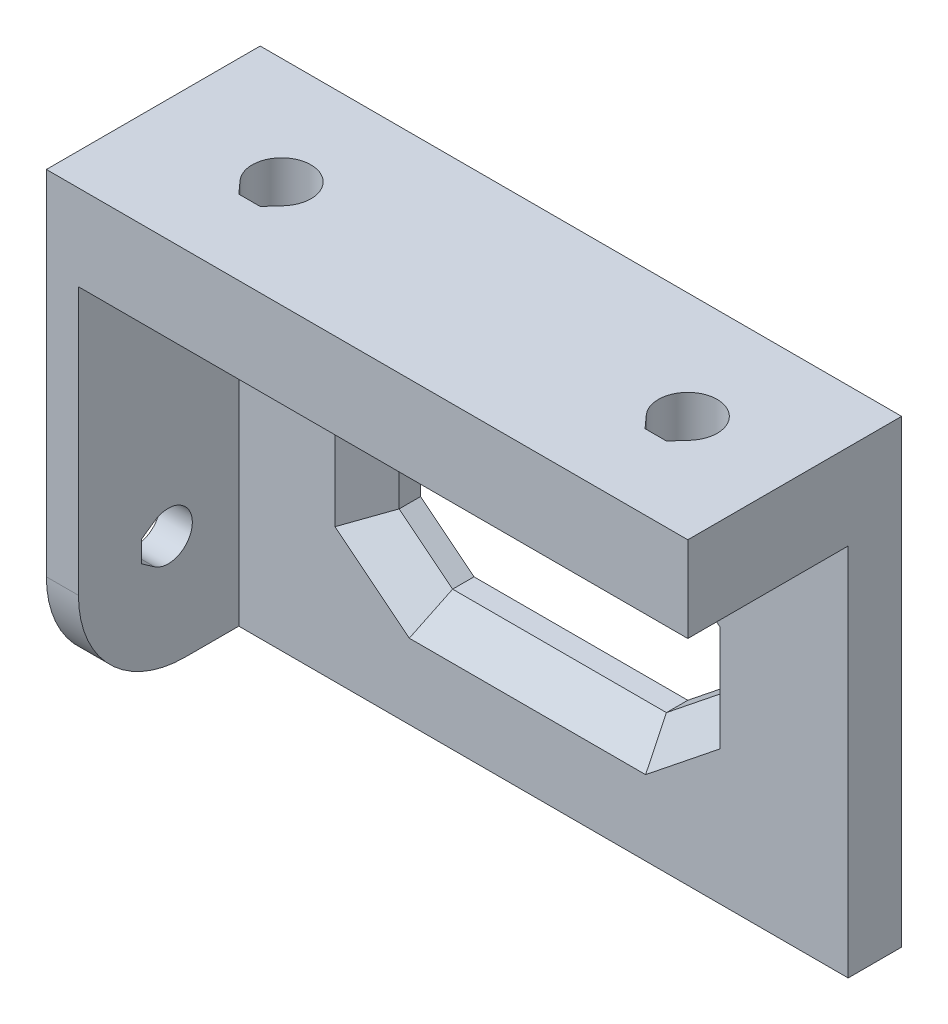
SolidWorks part; units mm, degrees
ref_plane "Alzado" through (0, 0, 0) normal (0, 0, 1) x (1, 0, 0)
ref_plane "Planta" through (0, 0, 0) normal (0, 1, 0) x (1, 0, 0)
ref_plane "Vista lateral" through (0, 0, 0) normal (1, 0, 0) x (0, 0, -1)
sketch "Croquis1" plane through (0, 0, 0) normal (0, 0, 1) x (1, 0, 0)
  line L1 (0, 0) -> (60, 0)
  line L2 (0, 0) -> (0, 35)
  line L3 (0, 35) -> (60, 35)
  line L4 (60, 0) -> (60, 35)
  line L5 (15, 25) -> (45, 25)
  line L6 (15, 25) -> (15, 10)
  line L7 (15, 10) -> (45, 10)
  line L8 (45, 25) -> (45, 10)
  dimension "D1" = 60
  dimension "D2" = 30
  dimension "D3" = 15
  dimension "D4" = 15
  dimension "D5" = 10
  dimension "D6" = 35
extrude "Saliente-Extruir1" add sketch "Croquis1" along normal blind 5
chamfer "Chaflán2" distance 4 distance2 5 2 edges at (45, 10, 2.5) (15, 25, 2.5)
chamfer "Chaflán3" distance 5 distance2 4 2 edges at (45, 25, 2.5) (15, 10, 2.5)
chamfer "Chaflán1" distance 3 angle 45 8 edges at (30, 10, 5) (45, 17.5, 5) (30, 25, 5) (15, 17.5, 5) (17.5, 12, 5) (42.5, 12, 5) (42.5, 23, 5) (17.5, 23, 5)
sketch "Croquis2" plane through (0, 0, 0) normal (0, 0, -1) x (-1, 0, 0)
  line L0 (0, 35) -> (0, 0) construction
  line L1 (-60, 35) -> (0, 35)
  line L2 (-60, 35) -> (-60, 43)
  line L3 (-60, 43) -> (0, 43)
  line L4 (0, 35) -> (0, 43)
  dimension "D1" = 8
extrude "Saliente-Extruir2" add sketch "Croquis2" against normal blind 20
sketch "Croquis3" plane through (0, 35, 0) normal (0, -1, 0) x (1, 0, 0)
  line L0 (60, 20) -> (0, 20) construction
  line L1 (9.9557, 11.8394) -> (11, 13)
  line L2 (11, 13) -> (13, 13)
  line L3 (13, 13) -> (14.0443, 11.8394)
  line L4 (12, 10) -> (12, 16.6449) construction
  line L5 (0, 20) -> (0, 5) construction
  line L6 (60, 20) -> (60, 5) construction
  line L7 (47.9557, 11.8394) -> (49, 13)
  line L8 (49, 13) -> (51, 13)
  line L9 (51, 13) -> (52.0443, 11.8394)
  line L10 (50, 10) -> (50, 14.7986) construction
  arc A0 (9.9557, 11.8394) -> (14.0443, 11.8394) centre (12, 10) ccw
  arc A1 (47.9557, 11.8394) -> (52.0443, 11.8394) centre (50, 10) ccw
  dimension "D2" = 5.5
  dimension "D1" = 10
  dimension "D3" = 3
  dimension "D4" = 2
  dimension "D5" = 12
  dimension "D6" = 10
  dimension "D7" = 3
  dimension "D8" = 2
extrude "Cortar-Extruir1" cut sketch "Croquis3" against normal through all
sketch "Croquis4" plane through (0, 0, 5) normal (0, 0, 1) x (1, 0, 0)
  line L0 (0, 0) -> (60, 0) construction
  line L1 (0, 35) -> (3, 35)
  line L2 (0, 35) -> (0, 0)
  line L3 (0, 0) -> (3, 0)
  line L4 (3, 35) -> (3, 0)
  dimension "D1" = 3
extrude "Saliente-Extruir3" add sketch "Croquis4" along normal up to surface (15 mm away) up to face at (30, 39, 20)
sketch "Croquis5" plane through (0, 0, 0) normal (-1, 0, 0) x (0, 0, 1)
  line L0 (20, 43) -> (0, 43) construction
  line L1 (0, 43) -> (0, 0) construction
  line L2 (11.6, 10.6) -> (16.9881, 10.6) construction
  line L3 (12.8867, 12.4458) -> (14.1, 11.6)
  line L4 (14.1, 11.6) -> (14.1, 9.6)
  line L5 (14.1, 9.6) -> (12.8867, 8.7542)
  arc A0 (12.8867, 12.4458) -> (12.8867, 8.7542) centre (11.6, 10.6) ccw
  dimension "D1" = 4.5
  dimension "D2" = 32.4
  dimension "D3" = 11.6
  dimension "D4" = 2.5
  dimension "D5" = 2
extrude "Cortar-Extruir2" cut sketch "Croquis5" against normal blind 10
fillet "Redondeo1" radius 10 1 edges at (1.5, 0, 20)
